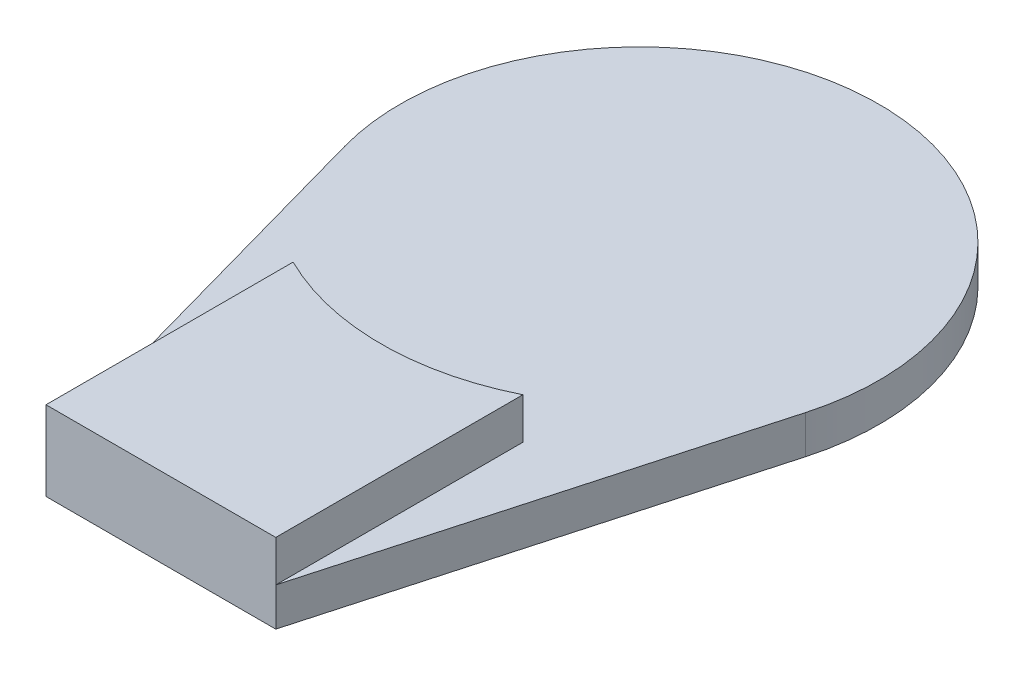
SolidWorks part; units mm, degrees
ref_plane "Front Plane" through (0, 0, 0) normal (0, 0, 1) x (1, 0, 0)
ref_plane "Top Plane" through (0, 0, 0) normal (0, 1, 0) x (1, 0, 0)
ref_plane "Right Plane" through (0, 0, 0) normal (1, 0, 0) x (0, 0, -1)
sketch "Sketch1" plane through (0, 0, 0) normal (0, 1, 0) x (1, 0, 0)
  line L0 (-12.0398, -3.3604) -> (-6, -25)
  line L1 (-6, -25) -> (6, -25)
  line L2 (6, -25) -> (12.0398, -3.3604)
  arc A0 (12.0398, -3.3604) -> (-12.0398, -3.3604) centre (0, 0) ccw
  dimension "D1" = 25
  dimension "D2" = 25
  dimension "D3" = 12
extrude "Boss-Extrude1" add sketch "Sketch1" along normal blind 2
sketch "Sketch2" plane through (0, 2, 0) normal (0, 1, 0) x (1, 0, 0)
  line L0 (6, -25) -> (12.0398, -3.3604) construction
  line L1 (-6, -25) -> (6, -25) construction
  line L2 (-12.0398, -3.3604) -> (-6, -25) construction
  line L3 (6, -25) -> (12.0398, -3.3604) construction
  line L4 (-6, -25) -> (6, -25) construction
  line L5 (-12.0398, -3.3604) -> (-6, -25) construction
  line L6 (-6, -25) -> (-6, -12.0934)
  line L7 (6, -25) -> (6, -12.0934)
  line L8 (-6, -25) -> (6, -25)
  circle A0 centre (0, 0) radius 13.5 construction
  arc A1 (-6, -12.0934) -> (6, -12.0934) centre (0, 0) ccw
  dimension "D1" = 27
extrude "Boss-Extrude2" add sketch "Sketch2" along normal blind 2.15
sketch "Sketch3" plane through (0, 0, 0) normal (0, -1, 0) x (1, 0, 0)
  circle A0 centre (0, 0) radius 8.5 construction
  circle A1 centre (0, 8.5) radius 1.15
  circle A2 centre (8.5, 0) radius 1.15
  circle A3 centre (0, -8.5) radius 1.15
  circle A4 centre (-8.5, 0) radius 1.15
  point P14 (0, 0)
  dimension "D1" = 17
  dimension "D2" = 2.3
  dimension "D3" = 4
